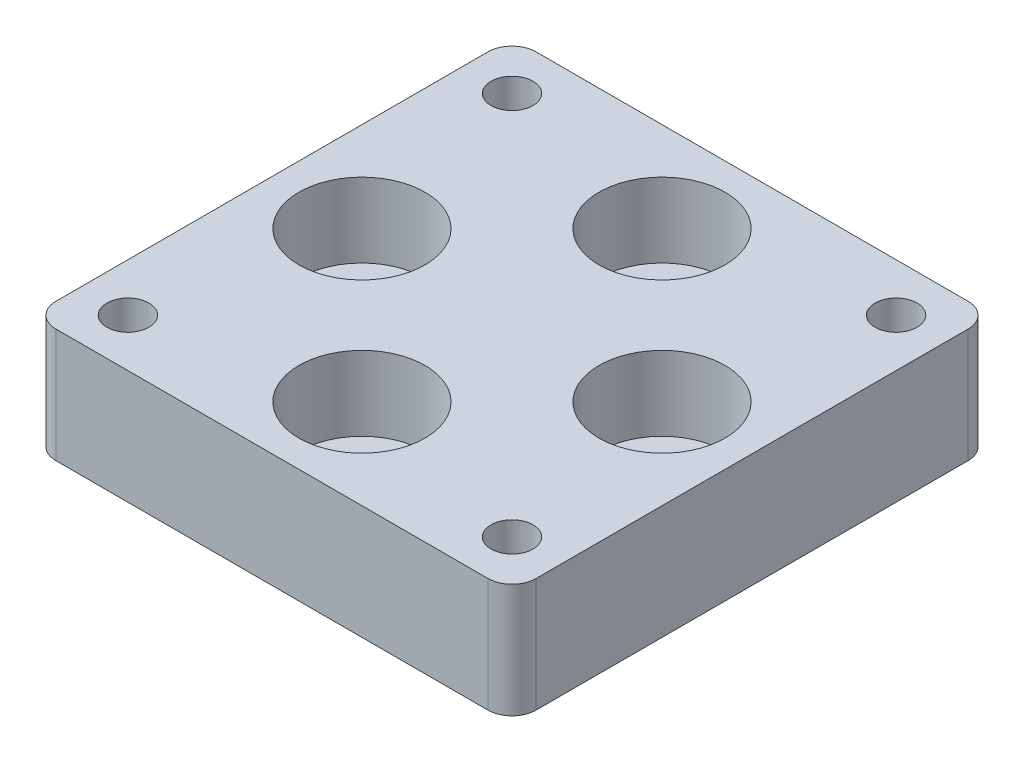
SolidWorks part; units mm, degrees
ref_plane "前视基准面" through (0, 0, 0) normal (0, 0, 1) x (1, 0, 0)
ref_plane "上视基准面" through (0, 0, 0) normal (0, 1, 0) x (1, 0, 0)
ref_plane "右视基准面" through (0, 0, 0) normal (1, 0, 0) x (0, 0, -1)
sketch "草图1" plane through (0, 0, 0) normal (0, 1, 0) x (1, 0, 0)
  line L17 (-20, -20) -> (20, -20)
  line L18 (-20, -20) -> (-20, 20)
  line L19 (-16, -16) -> (16, -16) construction
  line L20 (-16, -16) -> (-16, 16) construction
  line L21 (-16, 16) -> (16, 16) construction
  line L22 (16, -16) -> (16, 16) construction
  line L23 (0, 16) -> (0, -16) construction
  line L24 (-16, 0) -> (16, 0) construction
  line L25 (-20, 20) -> (20, 20)
  line L26 (20, -20) -> (20, 20)
  line L27 (0, 20) -> (0, -20) construction
  line L28 (-20, 0) -> (20, 0) construction
  circle A8 centre (-16, 16) radius 1.75
  circle A9 centre (16, 16) radius 1.75
  circle A10 centre (-16, -16) radius 1.75
  circle A13 centre (16, -16) radius 1.75
  circle A27 centre (-12.5, 0) radius 3.1
  circle A28 centre (12.5, 0) radius 3.1
  circle A30 centre (0, 12.5) radius 3.1
  circle A31 centre (0, -12.5) radius 3.1
  point P0 (0, 0)
  point P2 (0, 0)
  point P6 (0, 0)
  point P10 (0, 0)
  dimension "D3" = 40
  dimension "D4" = 6.2
  dimension "D5" = 25
  dimension "D6" = 25
  dimension "D1" = 3.5
  dimension "D2" = 32
extrude "凸台-拉伸1" add sketch "草图1" along normal blind 9.5
fillet "圆角1" radius 2 4 edges at (20, 4.75, -20) (20, 4.75, 20) (-20, 4.75, 20) (-20, 4.75, -20)
sketch "草图2" plane through (0, 9.5, 0) normal (0, 1, 0) x (1, 0, 0)
  circle A0 centre (0, 12.5) radius 5.25
  circle A1 centre (12.5, 0) radius 5.25
  circle A2 centre (0, -12.5) radius 5.25
  circle A3 centre (-12.5, 0) radius 5.25
  dimension "D1" = 10.5
extrude "切除-拉伸1" cut sketch "草图2" against normal blind 6.2
